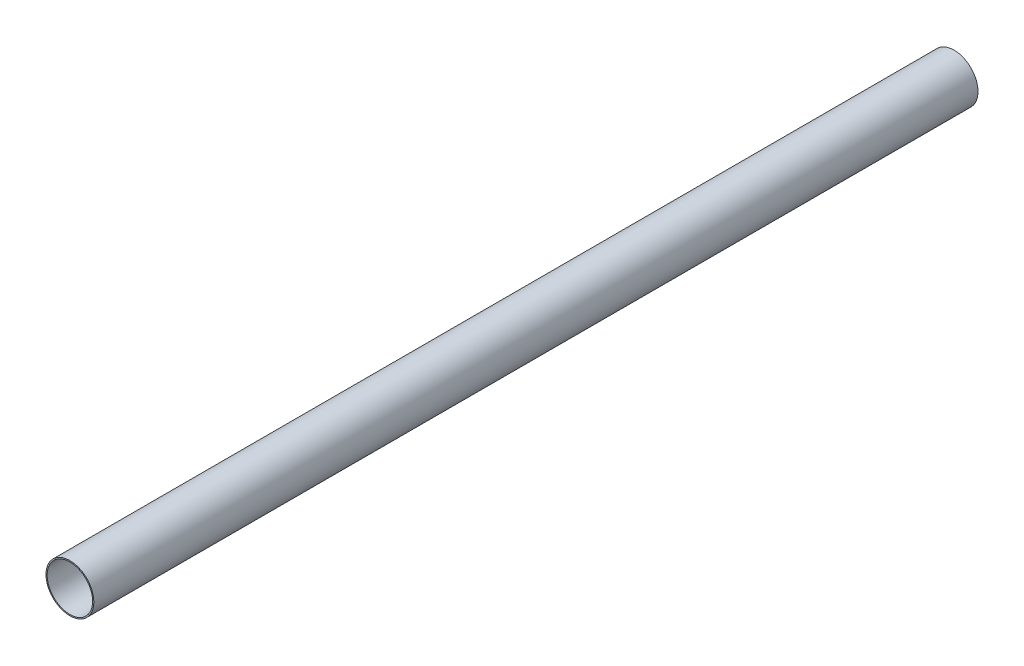
SolidWorks part; units mm, degrees
ref_plane "Front Plane" through (0, 0, 0) normal (0, 0, 1) x (1, 0, 0)
ref_plane "Top Plane" through (0, 0, 0) normal (0, 1, 0) x (1, 0, 0)
ref_plane "Right Plane" through (0, 0, 0) normal (1, 0, 0) x (0, 0, -1)
sketch "Sketch1" plane through (0, 0, 0) normal (0, 0, 1) x (1, 0, 0)
  circle A0 centre (0, 0) radius 15.265
  circle A1 centre (0, 0) radius 14.505
  dimension "D1" = 0.76
extrude "Boss-Extrude1" add sketch "Sketch1" along normal blind 563.88
